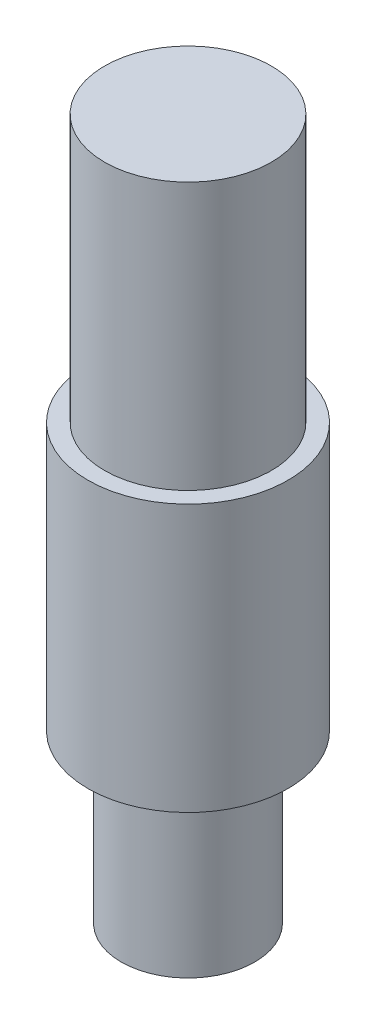
SolidWorks part; units mm, degrees
material "Plain Carbon Steel"
ref_plane "Front Plane" through (0, 0, 0) normal (0, 0, 1) x (1, 0, 0)
ref_plane "Top Plane" through (0, 0, 0) normal (0, 1, 0) x (1, 0, 0)
ref_plane "Right Plane" through (0, 0, 0) normal (1, 0, 0) x (0, 0, -1)
sketch "Sketch1" plane through (0, 0, 0) normal (0, 1, 0) x (1, 0, 0)
  circle A0 centre (0, 0) radius 10
  dimension "D1" = 20
extrude "Boss-Extrude3" add sketch "Sketch1" along normal blind 25
ref_plane "Plane2" through (0, 25, 0) normal (0, 1, 0) x (1, 0, 0)
sketch "Sketch5" plane through (0, 25, 0) normal (0, 1, 0) x (1, 0, 0)
  circle A0 centre (0, 0) radius 14.99
  dimension "D1" = 29.98
extrude "Boss-Extrude4" add sketch "Sketch5" along normal blind 40
ref_plane "Plane3" through (0, 65, 0) normal (0, 1, 0) x (1, 0, 0)
sketch "Sketch6" plane through (0, 65, 0) normal (0, 1, 0) x (1, 0, 0)
  circle A0 centre (0, 0) radius 12.49
  dimension "D1" = 24.98
extrude "Boss-Extrude5" add sketch "Sketch6" along normal blind 40
